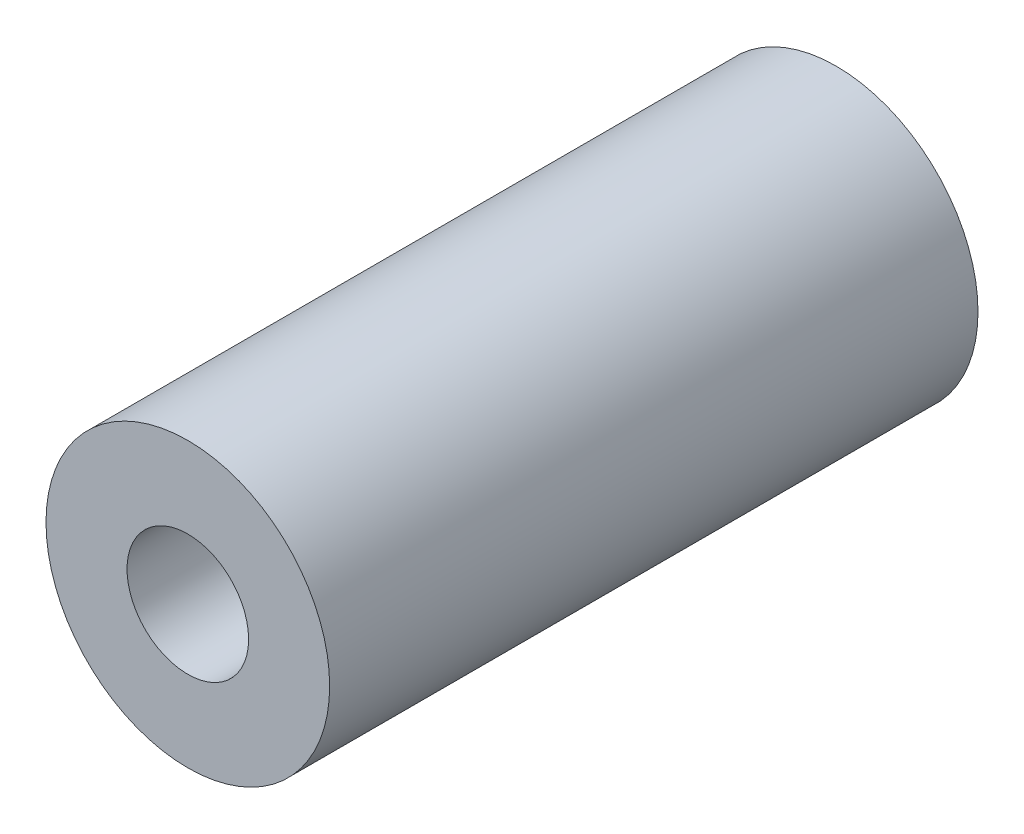
SolidWorks part; units mm, degrees
material "6061-T6 (SS)"
ref_plane "Front Plane" through (0, 0, 0) normal (0, 0, 1) x (1, 0, 0)
ref_plane "Top Plane" through (0, 0, 0) normal (0, 1, 0) x (1, 0, 0)
ref_plane "Right Plane" through (0, 0, 0) normal (1, 0, 0) x (0, 0, -1)
sketch "Sketch1" plane through (0, 0, 0) normal (0, 0, 1) x (1, 0, 0)
  circle A0 centre (0, 0) radius 11.1125
  circle A1 centre (0, 0) radius 4.7625
  dimension "D1" = 22.225
  dimension "D2" = 9.525
extrude "Boss-Extrude1" add sketch "Sketch1" along normal blind 50.8
